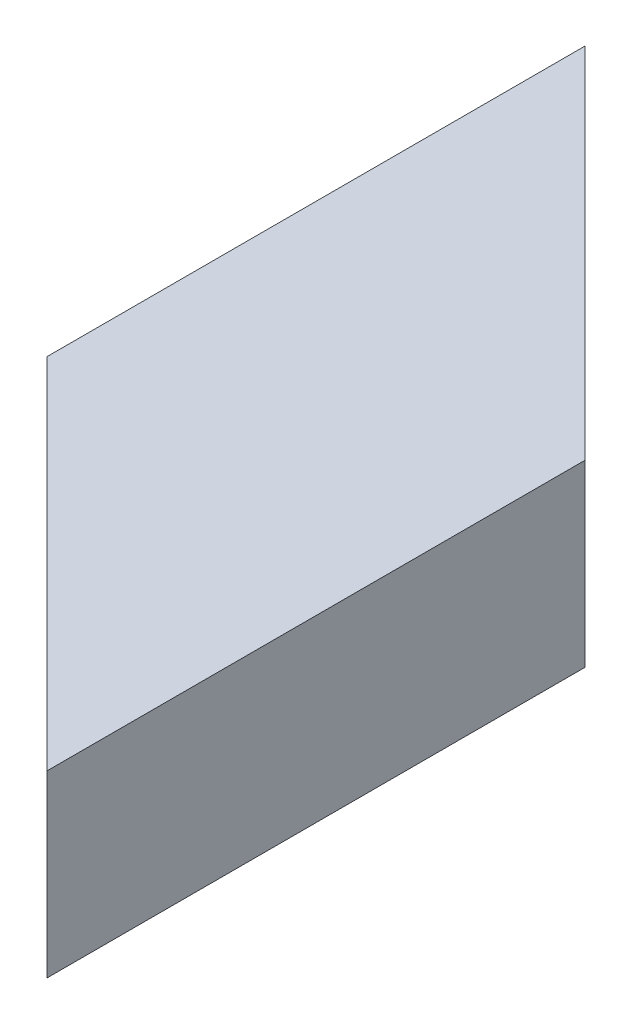
SolidWorks part; units mm, degrees
ref_plane "Front Plane" through (0, 0, 0) normal (0, 0, 1) x (1, 0, 0)
ref_plane "Top Plane" through (0, 0, 0) normal (0, 1, 0) x (1, 0, 0)
ref_plane "Right Plane" through (0, 0, 0) normal (1, 0, 0) x (0, 0, -1)
sketch "Sketch1" plane through (0, 0, 0) normal (0, 0, 1) x (1, 0, 0)
  line L1 (0, 0) -> (50.8, 0)
  line L2 (0, 0) -> (0, 25.4)
  line L3 (0, 25.4) -> (50.8, 25.4)
  line L4 (50.8, 0) -> (50.8, 25.4)
  line L5 (3.175, 3.175) -> (47.625, 3.175)
  line L6 (3.175, 3.175) -> (3.175, 22.225)
  line L7 (3.175, 22.225) -> (47.625, 22.225)
  line L8 (47.625, 3.175) -> (47.625, 22.225)
  dimension "D1" = 25.4
  dimension "D2" = 50.8
  dimension "D3" = 3.175
  dimension "D4" = 3.175
  dimension "D5" = 3.175
  dimension "D6" = 3.175
extrude "Boss-Extrude1" add sketch "Sketch1" along normal blind 127
sketch "Sketch2" plane through (0, 25.4, 0) normal (0, 1, 0) x (1, 0, 0)
  line L0 (0, 0) -> (50.8, -50.8)
  line L1 (50.8, -127) -> (50.8, 0) construction
  line L2 (50.8, -50.8) -> (50.8, 0)
  line L3 (50.8, 0) -> (0, 0)
  line L5 (0, -76.2) -> (0, -127)
  line L6 (0, -127) -> (0, 0) construction
  line L7 (0, -127) -> (50.8, -127)
  line L8 (50.8, -127) -> (0, -76.2)
  dimension "D1" = 45
  dimension "D2" = 45
extrude "Cut-Extrude1" cut sketch "Sketch2" against normal blind 127
